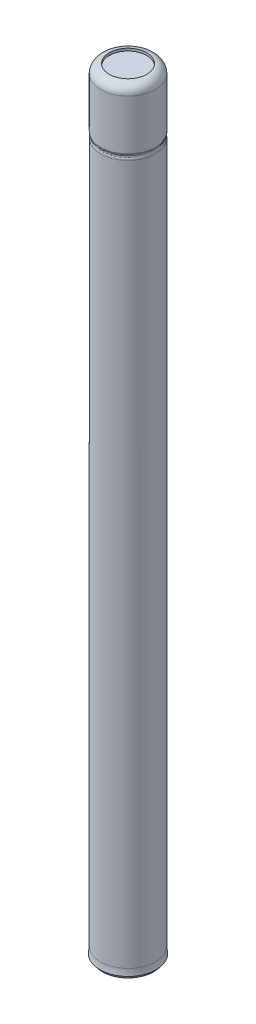
SolidWorks part; units mm, degrees
ref_plane "Front" through (0, 0, 0) normal (0, 0, 1) x (1, 0, 0)
ref_plane "Top" through (0, 0, 0) normal (0, 1, 0) x (1, 0, 0)
ref_plane "Right" through (0, 0, 0) normal (1, 0, 0) x (0, 0, -1)
sketch "Sketch2" plane through (0, 0, 0) normal (0, 0, 1) x (1, 0, 0)
  line L0 (0, 0) -> (0, 263.525) construction
  line L1 (0, 263.525) -> (9.34, 263.525)
  line L2 (9.34, 263.525) -> (9.34, 243.38)
  line L3 (9.0007, 0) -> (0, 0)
  line L4 (9.34, 241.67) -> (9.0007, 242.525)
  line L5 (9.0007, 242.525) -> (9.34, 243.38)
  line L6 (9.34, 241.67) -> (9.34, 3.4106)
  line L7 (9.5468, 1.2) -> (9.0007, 1.2)
  line L8 (9.0007, 1.2) -> (9.0007, 0)
  line L9 (0, 0) -> (0, 263.525)
  arc A0 (9.34, 3.4106) -> (9.5468, 1.2) centre (21.259, 3.4106) ccw
  point P5 (9.7358, 0.8907)
  point P11 (9.4078, 0.8741)
  point P14 (9.5468, 1.2)
  point P15 (9.34, 3.4106)
  dimension "D1" = 9.34
  dimension "D2" = 1.2
  dimension "D3" = 21
  dimension "D4" = 263.525
revolve "Revolve1" add sketch "Sketch2" angle 360 about L0
fillet "Fillet1" radius 3 1 edges at (9.34, 263.525, 0)
fillet "Fillet2" radius 0.75 4 edges at (9.0007, 0, 0) (9.34, 243.38, 0) (9.0007, 242.525, 0) (9.34, 241.67, 0)
sketch "Sketch3" plane through (0, 263.525, 0) normal (0, 1, 0) x (1, 0, 0)
  circle A0 centre (0, 0) radius 6.38
extrude "Cut-Extrude1" cut sketch "Sketch3" against normal blind 0.85
